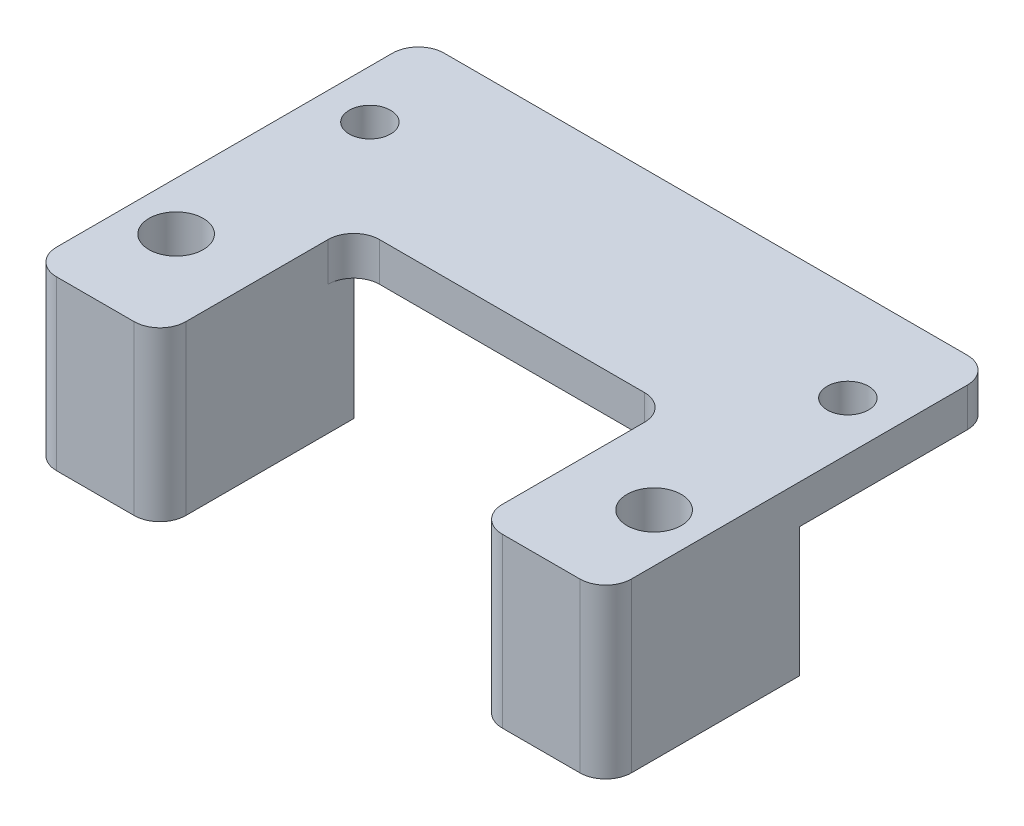
SolidWorks part; units mm, degrees
ref_plane "正面" through (0, 0, 0) normal (0, 0, 1) x (1, 0, 0)
ref_plane "平面" through (0, 0, 0) normal (0, 1, 0) x (1, 0, 0)
ref_plane "右側面" through (0, 0, 0) normal (1, 0, 0) x (0, 0, -1)
sketch "ｽｹｯﾁ1" plane through (0, 0, 0) normal (0, 1, 0) x (1, 0, 0)
  line L1 (0, 0) -> (44.5, 0)
  line L2 (0, 0) -> (0, 30)
  line L3 (0, 30) -> (44.5, 30)
  line L4 (44.5, 0) -> (44.5, 30)
  dimension "D1" = 30
  dimension "D2" = 44.5
extrude "ﾎﾞｽ - 押し出し1" add sketch "ｽｹｯﾁ1" along normal blind 3
sketch "ｽｹｯﾁ2" plane through (0, 0, 0) normal (0, -1, 0) x (-1, 0, 0)
  line L1 (0, 0) -> (-10, 0)
  line L2 (0, 0) -> (0, 15)
  line L3 (0, 15) -> (-10, 15)
  line L4 (-10, 0) -> (-10, 15)
  line L5 (-44.5, 0) -> (-34.5, 0)
  line L6 (-44.5, 0) -> (-44.5, 15)
  line L7 (-44.5, 15) -> (-34.5, 15)
  line L8 (-34.5, 0) -> (-34.5, 15)
  dimension "D1" = 10
  dimension "D2" = 15
  dimension "D3" = 10
extrude "ﾎﾞｽ - 押し出し2" add sketch "ｽｹｯﾁ2" along normal blind 10
sketch "ｽｹｯﾁ3" plane through (0, 3, 0) normal (0, 1, 0) x (1, 0, 0)
  line L0 (0, 30) -> (0, 0) construction
  line L1 (0, 0) -> (44.5, 0) construction
  line L2 (44.5, 30) -> (0, 30) construction
  line L3 (44.5, 0) -> (44.5, 30) construction
  circle A0 centre (3.75, 7.5) radius 2.1
  circle A1 centre (40.75, 7.5) radius 2.1
  circle A2 centre (40.75, 22.5) radius 1.6
  circle A3 centre (3.75, 22.5) radius 1.6
  dimension "D1" = 3.75
  dimension "D2" = 7.5
  dimension "D3" = 4.2
  dimension "D6" = 3.75
  dimension "D7" = 7.5
  dimension "D8" = 3.75
  dimension "D4" = 3.2
  dimension "D5" = 3.2
  dimension "D9" = 4.2
  dimension "D10" = 7.5
  dimension "D11" = 3.2
  dimension "D13" = 3.75
  dimension "D12" = 7.5
extrude "ｶｯﾄ - 押し出し1" cut sketch "ｽｹｯﾁ3" against normal blind 45
sketch "ｽｹｯﾁ4" plane through (0, 0, 0) normal (0, -1, 0) x (-1, 0, 0)
  line L1 (-10, 0) -> (-34.5, 0)
  line L2 (-10, 0) -> (-10, 15)
  line L3 (-10, 15) -> (-34.5, 15)
  line L4 (-34.5, 0) -> (-34.5, 15)
extrude "ｶｯﾄ - 押し出し2" cut sketch "ｽｹｯﾁ4" against normal blind 10
fillet "ﾌｨﾚｯﾄ2" radius 2 8 edges at (10, -3.5, 0) (34.5, -3.5, 0) (10, 1.5, -15) (34.5, 1.5, -15) (0, 1.5, -30) (44.5, 1.5, -30) (44.5, -3.5, 0) (0, -3.5, 0)
